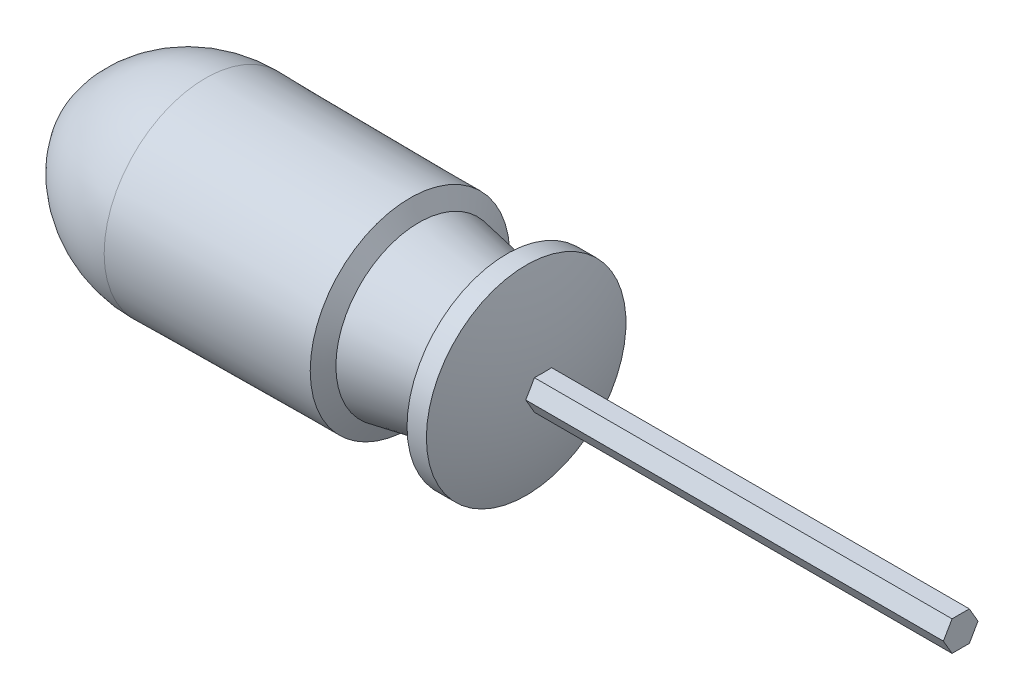
SolidWorks part; units mm, degrees
ref_plane "Front Plane" through (0, 0, 0) normal (0, 0, 1) x (1, 0, 0)
ref_plane "Top Plane" through (0, 0, 0) normal (0, 1, 0) x (1, 0, 0)
ref_plane "Right Plane" through (0, 0, 0) normal (1, 0, 0) x (0, 0, -1)
sketch "Sketch1" plane through (0, 0, 0) normal (0, 0, 1) x (1, 0, 0)
  line L0 (-90.0821, 0) -> (98.904, 0) construction
  line L1 (0, 53.4219) -> (0, -63.8122) construction
  line L2 (-60.4974, 0) -> (39.5026, 0)
  line L3 (35.7417, 21.6482) -> (31.5417, 21.6482)
  line L5 (29.7831, 14.8) -> (12.4635, 18)
  line L6 (12.4635, 18) -> (10.5417, 21.6482)
  line L7 (10.5417, 21.6482) -> (-33.8108, 21.995)
  line L8 (-50, 0) -> (39.5026, 0)
  arc A0 (39.5026, 0) -> (35.7417, 21.6482) centre (-24.6825, 0) ccw
  arc A2 (-33.8108, 21.995) -> (-60.1986, 6.6932) centre (-34.0454, -8.004) ccw
  arc A3 (-60.1986, 6.6932) -> (-60.4974, 0) centre (-53.7166, 3.0505) ccw
  arc A4 (31.5417, 21.6482) -> (29.7831, 14.8) centre (17.328, 21.6482) cw
  point P19 (-25.4538, 20.5014)
  point P20 (0, -5.1952)
  point P21 (-27.4423, 20.5014)
  point P22 (11.5026, 19.8241)
  point P23 (21.8573, 13.3623)
  point P24 (17.6774, 13.3623)
  point P25 (-52.6495, 4.8979)
  point P26 (14.229, 20.5014)
  point P27 (20.7727, 13.7447)
  point P28 (-44.9856, 14.8)
  point P29 (10.6907, 19.3873)
  point P30 (13.7003, 11.4876)
  point P31 (-48.4092, 13.7447)
  point P32 (6.4774, 17.5928)
  point P33 (10.3898, 8.9295)
  point P34 (27.9955, 14.8)
  point P35 (27.8451, 14.8)
  point P36 (27.6511, 14.8)
  point P37 (0, 0)
  point P38 (29.1875, 14.8)
  point P39 (29.9557, 14.8)
  point P40 (10.5353, 11.8901)
  point P41 (0, 0)
  point P42 (-37.145, 17.4472)
  point P43 (0, 0)
  point P44 (7.6485, 17.5928)
  point P45 (11.367, 14.8)
  point P46 (8.4469, 24.041)
  point P47 (0, 0)
  point P48 (23.9683, 20.2063)
  point P49 (-54.055, 18)
  point P50 (8.4469, 28.3571)
  point P51 (29.9529, 26.257)
  point P52 (0, 0)
  point P53 (0, 0)
  point P54 (0, 0)
  point P55 (0, 0)
  point P56 (-33.1704, 27.4008)
  point P57 (9.3219, 26.257)
  point P58 (-35.3123, 26.257)
  point P59 (9.893, 26.257)
  point P60 (26.1101, 14.8)
  point P61 (12.2715, 18)
  point P62 (9.893, 18)
  point P63 (29.8941, 14.8)
  point P64 (46.6519, 21.6482)
  point P65 (12.4635, 21.6482)
  point P66 (-34.0532, 22.1808)
  point P67 (-41.6776, 22.5131)
  point P68 (11.2985, 21.6482)
  point P69 (-34.0454, 21.7437)
  point P70 (10.5417, 21.6482)
  point P71 (50, 0)
  point P72 (50, 0)
  point P73 (0, 0)
  point P74 (50, 0)
  point P75 (0, 0)
  point P76 (0, 0)
  point P77 (0, 0)
  point P78 (0, 0)
  point P79 (0, 0)
  dimension "D1" = 14.8
  dimension "D3" = 30
  dimension "D2" = 72
  dimension "D4" = 100
  dimension "D5" = 50
  dimension "D6" = 21
  dimension "D7" = 18
  dimension "D8" = 4.2
revolve "Revolve1" add sketch "Sketch1" angle 360 about L0
sketch "Sketch2" plane through (0, 0, 0) normal (1, 0, 0) x (0, 0, -1)
  line L0 (-29.9193, 0) -> (37.5941, 0) construction
  line L1 (0, 22.9309) -> (0, -24.4284) construction
  line L3 (3.7528, 0) -> (1.8764, 3.25)
  line L4 (1.8764, 3.25) -> (-1.8764, 3.25)
  line L5 (-1.8764, 3.25) -> (-3.7528, 0)
  line L6 (-3.7528, 0) -> (-1.8764, -3.25)
  line L7 (-1.8764, -3.25) -> (1.8764, -3.25)
  line L8 (1.8764, -3.25) -> (3.7528, 0)
  circle A0 centre (0, 0) radius 3.25 construction
  dimension "D1" = 6.5
extrude "Boss-Extrude1" add sketch "Sketch2" along normal blind 130
